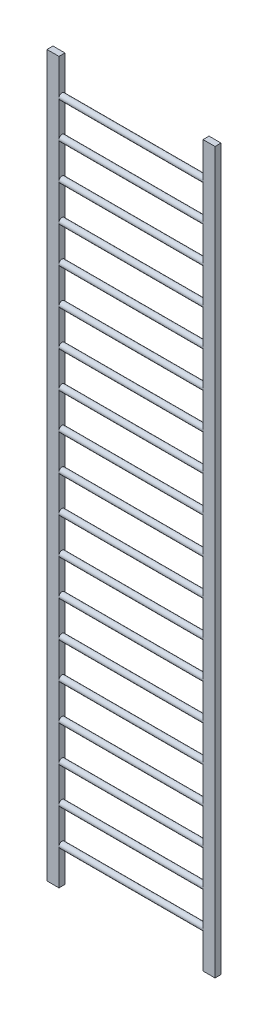
SolidWorks part; units mm, degrees
ref_plane "Plano frontal" through (0, 0, 0) normal (0, 0, 1) x (1, 0, 0)
ref_plane "Plano superior" through (0, 0, 0) normal (0, 1, 0) x (1, 0, 0)
ref_plane "Plano direito" through (0, 0, 0) normal (1, 0, 0) x (0, 0, -1)
sketch "Esboço1" plane through (0, 0, 0) normal (0, 1, 0) x (1, 0, 0)
  line L0 (0, 0) -> (0, 384.4945) construction
  line L1 (600, -25) -> (700, -25)
  line L2 (600, -25) -> (600, 25)
  line L3 (600, 25) -> (700, 25)
  line L4 (700, -25) -> (700, 25)
  line L5 (-700, -25) -> (-700, 25)
  line L6 (-600, 25) -> (-700, 25)
  line L7 (-600, -25) -> (-600, 25)
  line L8 (-600, -25) -> (-700, -25)
  point P11 (600, 0)
  dimension "D1" = 100
  dimension "D2" = 50
  dimension "D3" = 700
extrude "Ressalto-extrusão1" add sketch "Esboço1" along normal blind 6000
sketch "Esboço4" plane through (0, 0, 0) normal (1, 0, 0) x (0, 0, -1)
  line L0 (25, 6000) -> (25, 0) construction
  line L1 (-25, 6000) -> (-25, 0) construction
  circle A0 centre (0, 300) radius 25
  circle A1 centre (0, 600) radius 25
  circle A2 centre (0, 900) radius 25
  circle A3 centre (0, 1200) radius 25
  circle A4 centre (0, 1500) radius 25
  circle A5 centre (0, 1800) radius 25
  circle A6 centre (0, 2100) radius 25
  circle A7 centre (0, 2400) radius 25
  circle A8 centre (0, 2700) radius 25
  circle A9 centre (0, 3000) radius 25
  circle A10 centre (0, 3300) radius 25
  circle A11 centre (0, 3600) radius 25
  circle A12 centre (0, 3900) radius 25
  circle A13 centre (0, 4200) radius 25
  circle A14 centre (0, 4500) radius 25
  circle A15 centre (0, 4800) radius 25
  circle A16 centre (0, 5100) radius 25
  circle A17 centre (0, 5400) radius 25
  circle A18 centre (0, 5700) radius 25
  dimension "D1" = 300
  dimension "D2" = 19
extrude "Ressalto-extrusão3" add sketch "Esboço4" along normal up to next (600 mm away) and the other way up to next (700 mm away) contours A0
